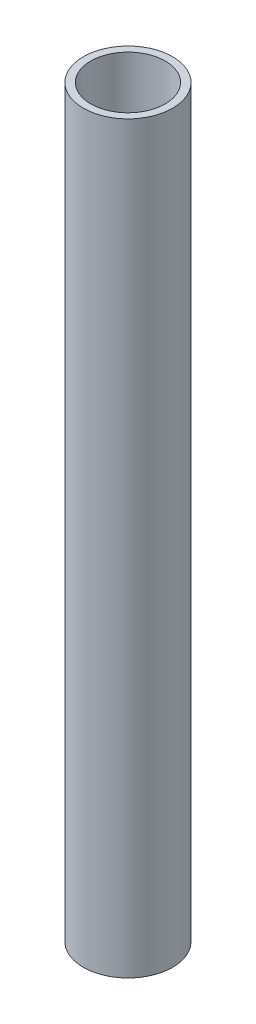
SolidWorks part; units mm, degrees
ref_plane "Front Plane" through (0, 0, 0) normal (0, 0, 1) x (1, 0, 0)
ref_plane "Top Plane" through (0, 0, 0) normal (0, 1, 0) x (1, 0, 0)
ref_plane "Right Plane" through (0, 0, 0) normal (1, 0, 0) x (0, 0, -1)
sketch "Sketch1" plane through (0, 0, 0) normal (0, 1, 0) x (1, 0, 0)
  circle A0 centre (0, 0) radius 3
  circle A1 centre (0, 0) radius 2.5
extrude "Boss-Extrude1" add sketch "Sketch1" along normal blind 50
